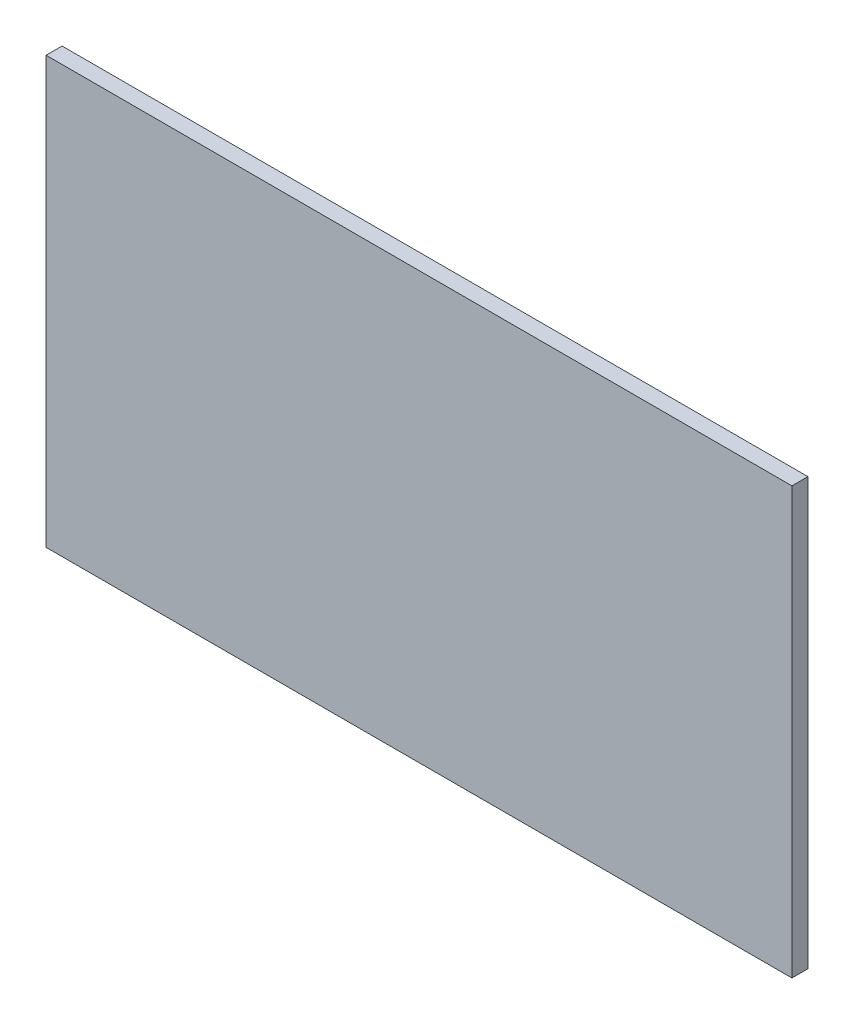
SolidWorks part; units mm, degrees
ref_plane "Front Plane" through (0, 0, 0) normal (0, 0, 1) x (1, 0, 0)
ref_plane "Top Plane" through (0, 0, 0) normal (0, 1, 0) x (1, 0, 0)
ref_plane "Right Plane" through (0, 0, 0) normal (1, 0, 0) x (0, 0, -1)
sketch "Sketch2" plane through (0, 0, 0) normal (0, 0, 1) x (1, 0, 0)
  line L1 (0, 0) -> (140, 0)
  line L2 (0, 0) -> (0, -80)
  line L3 (0, -80) -> (140, -80)
  line L4 (140, 0) -> (140, -80)
  dimension "D1" = 80
  dimension "D2" = 140
extrude "Boss-Extrude1" add sketch "Sketch2" along normal blind 3
